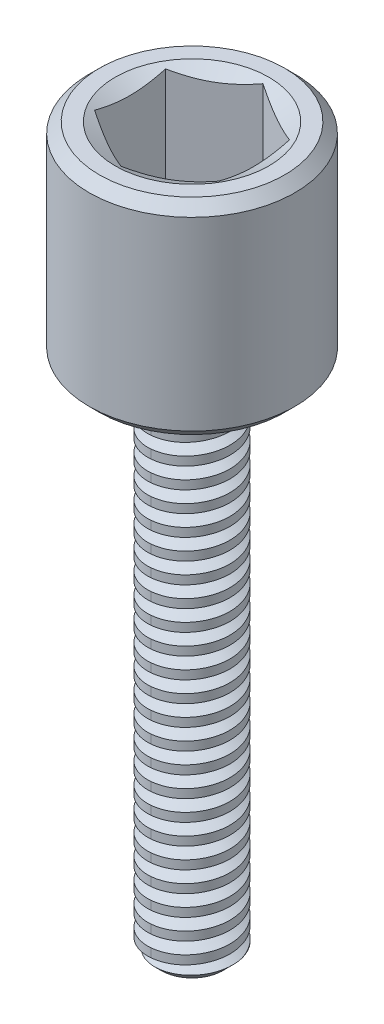
SolidWorks part; units mm, degrees
ref_plane "Front Plane" through (0, 0, 0) normal (0, 0, 1) x (1, 0, 0)
ref_plane "Top Plane" through (0, 0, 0) normal (0, 1, 0) x (1, 0, 0)
ref_plane "Right Plane" through (0, 0, 0) normal (1, 0, 0) x (0, 0, -1)
sketch "Sketch1" plane through (0, 0, 0) normal (0, 1, 0) x (1, 0, 0)
  circle A0 centre (0, 0) radius 2.54
extrude "Boss-Extrude1" add sketch "Sketch1" along normal blind 5.08
sketch "Sketch2" plane through (0, 0, 0) normal (0, -1, 0) x (1, 0, 0)
  circle A0 centre (0, 0) radius 1.016
extrude "Boss-Extrude2" add sketch "Sketch2" along normal blind 12.7
chamfer "Chamfer1" distance 0.254 angle 45 1 edges at (0, -12.7, -1.016)
sketch "Sketch4" plane through (0, -12.7, 0) normal (0, -1, 0) x (1, 0, 0)
  circle A0 centre (0, 0) radius 1.016 construction
  circle A1 centre (0, 0) radius 1.016
curve "Helix/Spiral1" pitch 0.508 height 12.7 turns 25
sketch "Sketch5" plane through (0, 0, 0) normal (1, 0, 0) x (0, 0, -1)
  line L0 (1.0802, -12.5163) -> (1.0802, -12.8837)
  line L1 (1.0802, -12.8837) -> (0.762, -12.7)
  line L2 (0.762, -12.7) -> (1.0802, -12.5163)
  line L3 (0, -12.2555) -> (0, -14.0004) construction
  spline S0 degree 3 poles (-0.7184, -12.7) (-0.8119, -12.6895) (-0.9634, -12.6682) (-1.0424, -12.6365) (-0.9631, -12.6047) (-0.7371, -12.573) (-0.3989, -12.5412) (0, -12.5095) (0.3989, -12.4777) (0.7371, -12.446) (0.9631, -12.4142) (1.0425, -12.3825) (0.9631, -12.3507) (0.7371, -12.319) (0.3989, -12.2872) (0, -12.2555) (-0.3989, -12.2237) (-0.7371, -12.192) (-0.9631, -12.1602) (-1.0425, -12.1285) (-0.9631, -12.0967) (-0.7371, -12.065) (-0.3989, -12.0332) (0, -12.0015) (0.3989, -11.9698) (0.7371, -11.938) (0.9631, -11.9062) (1.0425, -11.8745) (0.9631, -11.8428) (0.7371, -11.811) (0.3989, -11.7793) (0, -11.7475) (-0.3989, -11.7157) (-0.7371, -11.684) (-0.9631, -11.6523) (-1.0425, -11.6205) (-0.9631, -11.5888) (-0.7371, -11.557) (-0.3989, -11.5253) (0, -11.4935) (0.3989, -11.4618) (0.7371, -11.43) (0.9631, -11.3982) (1.0425, -11.3665) (0.9631, -11.3348) (0.7371, -11.303) (0.3989, -11.2713) (0, -11.2395) (-0.3989, -11.2078) (-0.7371, -11.176) (-0.9631, -11.1442) (-1.0425, -11.1125) (-0.9631, -11.0807) (-0.7371, -11.049) (-0.3989, -11.0172) (0, -10.9855) (0.3989, -10.9537) (0.7371, -10.922) (0.9631, -10.8902) (1.0425, -10.8585) (0.9631, -10.8267) (0.7371, -10.795) (0.3989, -10.7632) (0, -10.7315) (-0.3989, -10.6997) (-0.7371, -10.668) (-0.9631, -10.6362) (-1.0425, -10.6045) (-0.9631, -10.5727) (-0.7371, -10.541) (-0.3989, -10.5092) (0, -10.4775) (0.3989, -10.4457) (0.7371, -10.414) (0.9631, -10.3822) (1.0425, -10.3505) (0.9631, -10.3187) (0.7371, -10.287) (0.3989, -10.2552) (0, -10.2235) (-0.3989, -10.1917) (-0.7371, -10.16) (-0.9631, -10.1282) (-1.0425, -10.0965) (-0.9631, -10.0647) (-0.7371, -10.033) (-0.3989, -10.0012) (0, -9.9695) (0.3989, -9.9377) (0.7371, -9.906) (0.9631, -9.8742) (1.0425, -9.8425) (0.9631, -9.8107) (0.7371, -9.779) (0.3989, -9.7472) (0, -9.7155) (-0.3989, -9.6837) (-0.7371, -9.652) (-0.9631, -9.6202) (-1.0425, -9.5885) (-0.9631, -9.5567) (-0.7371, -9.525) (-0.3989, -9.4932) (0, -9.4615) (0.3989, -9.4297) (0.7371, -9.398) (0.9631, -9.3662) (1.0425, -9.3345) (0.9631, -9.3027) (0.7371, -9.271) (0.3989, -9.2392) (0, -9.2075) (-0.3989, -9.1757) (-0.7371, -9.144) (-0.9631, -9.1122) (-1.0425, -9.0805) (-0.9631, -9.0487) (-0.7371, -9.017) (-0.3989, -8.9852) (0, -8.9535) (0.3989, -8.9217) (0.7371, -8.89) (0.9631, -8.8582) (1.0425, -8.8265) (0.9631, -8.7947) (0.7371, -8.763) (0.3989, -8.7312) (0, -8.6995) (-0.3989, -8.6677) (-0.7371, -8.636) (-0.9631, -8.6042) (-1.0425, -8.5725) (-0.9631, -8.5407) (-0.7371, -8.509) (-0.3989, -8.4772) (0, -8.4455) (0.3989, -8.4137) (0.7371, -8.382) (0.9631, -8.3502) (1.0425, -8.3185) (0.9631, -8.2867) (0.7371, -8.255) (0.3989, -8.2232) (0, -8.1915) (-0.3989, -8.1597) (-0.7371, -8.128) (-0.9631, -8.0962) (-1.0425, -8.0645) (-0.9631, -8.0327) (-0.7371, -8.001) (-0.3989, -7.9693) (0, -7.9375) (0.3989, -7.9057) (0.7371, -7.874) (0.9631, -7.8423) (1.0425, -7.8105) (0.9631, -7.7788) (0.7371, -7.747) (0.3989, -7.7153) (0, -7.6835) (-0.3989, -7.6518) (-0.7371, -7.62) (-0.9631, -7.5883) (-1.0425, -7.5565) (-0.9631, -7.5248) (-0.7371, -7.493) (-0.3989, -7.4613) (0, -7.4295) (0.3989, -7.3978) (0.7371, -7.366) (0.9631, -7.3343) (1.0425, -7.3025) (0.9631, -7.2708) (0.7371, -7.239) (0.3989, -7.2073) (0, -7.1755) (-0.3989, -7.1438) (-0.7371, -7.112) (-0.9631, -7.0803) (-1.0425, -7.0485) (-0.9631, -7.0168) (-0.7371, -6.985) (-0.3989, -6.9533) (0, -6.9215) (0.3989, -6.8898) (0.7371, -6.858) (0.9631, -6.8263) (1.0425, -6.7945) (0.9631, -6.7628) (0.7371, -6.731) (0.3989, -6.6993) (0, -6.6675) (-0.3989, -6.6358) (-0.7371, -6.604) (-0.9631, -6.5723) (-1.0425, -6.5405) (-0.9631, -6.5088) (-0.7371, -6.477) (-0.3989, -6.4453) (0, -6.4135) (0.3989, -6.3818) (0.7371, -6.35) (0.9631, -6.3183) (1.0425, -6.2865) (0.9631, -6.2548) (0.7371, -6.223) (0.3989, -6.1913) (0, -6.1595) (-0.3989, -6.1278) (-0.7371, -6.096) (-0.9631, -6.0643) (-1.0425, -6.0325) (-0.9631, -6.0008) (-0.7371, -5.969) (-0.3989, -5.9373) (0, -5.9055) (0.3989, -5.8738) (0.7371, -5.842) (0.9631, -5.8103) (1.0425, -5.7785) (0.9631, -5.7468) (0.7371, -5.715) (0.3989, -5.6833) (0, -5.6515) (-0.3989, -5.6198) (-0.7371, -5.588) (-0.9631, -5.5563) (-1.0425, -5.5245) (-0.9631, -5.4928) (-0.7371, -5.461) (-0.3989, -5.4293) (0, -5.3975) (0.3989, -5.3658) (0.7371, -5.334) (0.9631, -5.3023) (1.0425, -5.2705) (0.9631, -5.2388) (0.7371, -5.207) (0.3989, -5.1753) (0, -5.1435) (-0.3989, -5.1118) (-0.7371, -5.08) (-0.9631, -5.0483) (-1.0425, -5.0165) (-0.9631, -4.9848) (-0.7371, -4.953) (-0.3989, -4.9213) (0, -4.8895) (0.3989, -4.8578) (0.7371, -4.826) (0.9631, -4.7943) (1.0425, -4.7625) (0.9631, -4.7308) (0.7371, -4.699) (0.3989, -4.6673) (0, -4.6355) (-0.3989, -4.6038) (-0.7371, -4.572) (-0.9631, -4.5403) (-1.0425, -4.5085) (-0.9631, -4.4768) (-0.7371, -4.445) (-0.3989, -4.4133) (0, -4.3815) (0.3989, -4.3498) (0.7371, -4.318) (0.9631, -4.2863) (1.0425, -4.2545) (0.9631, -4.2228) (0.7371, -4.191) (0.3989, -4.1593) (0, -4.1275) (-0.3989, -4.0958) (-0.7371, -4.064) (-0.9631, -4.0323) (-1.0425, -4.0005) (-0.9631, -3.9688) (-0.7371, -3.937) (-0.3989, -3.9053) (0, -3.8735) (0.3989, -3.8418) (0.7371, -3.81) (0.9631, -3.7783) (1.0425, -3.7465) (0.9631, -3.7148) (0.7371, -3.683) (0.3989, -3.6513) (0, -3.6195) (-0.3989, -3.5878) (-0.7371, -3.556) (-0.9631, -3.5243) (-1.0425, -3.4925) (-0.9631, -3.4608) (-0.7371, -3.429) (-0.3989, -3.3973) (0, -3.3655) (0.3989, -3.3338) (0.7371, -3.302) (0.9631, -3.2703) (1.0425, -3.2385) (0.9631, -3.2068) (0.7371, -3.175) (0.3989, -3.1433) (0, -3.1115) (-0.3989, -3.0798) (-0.7371, -3.048) (-0.9631, -3.0163) (-1.0425, -2.9845) (-0.9631, -2.9527) (-0.7371, -2.921) (-0.3989, -2.8893) (0, -2.8575) (0.3989, -2.8257) (0.7371, -2.794) (0.9631, -2.7622) (1.0425, -2.7305) (0.9631, -2.6987) (0.7371, -2.667) (0.3989, -2.6352) (0, -2.6035) (-0.3989, -2.5717) (-0.7371, -2.54) (-0.9631, -2.5082) (-1.0425, -2.4765) (-0.9631, -2.4447) (-0.7371, -2.413) (-0.3989, -2.3812) (0, -2.3495) (0.3989, -2.3177) (0.7371, -2.286) (0.9631, -2.2542) (1.0425, -2.2225) (0.9631, -2.1907) (0.7371, -2.159) (0.3989, -2.1272) (0, -2.0955) (-0.3989, -2.0637) (-0.7371, -2.032) (-0.9631, -2.0002) (-1.0425, -1.9685) (-0.9631, -1.9367) (-0.7371, -1.905) (-0.3989, -1.8732) (0, -1.8415) (0.3989, -1.8097) (0.7371, -1.778) (0.9631, -1.7462) (1.0425, -1.7145) (0.9631, -1.6827) (0.7371, -1.651) (0.3989, -1.6192) (0, -1.5875) (-0.3989, -1.5557) (-0.7371, -1.524) (-0.9631, -1.4922) (-1.0425, -1.4605) (-0.9631, -1.4287) (-0.7371, -1.397) (-0.3989, -1.3652) (0, -1.3335) (0.3989, -1.3017) (0.7371, -1.27) (0.9631, -1.2382) (1.0425, -1.2065) (0.9631, -1.1747) (0.7371, -1.143) (0.3989, -1.1112) (0, -1.0795) (-0.3989, -1.0477) (-0.7371, -1.016) (-0.9631, -0.9842) (-1.0425, -0.9525) (-0.9631, -0.9207) (-0.7371, -0.889) (-0.3989, -0.8572) (0, -0.8255) (0.3989, -0.7937) (0.7371, -0.762) (0.9631, -0.7302) (1.0425, -0.6985) (0.9631, -0.6667) (0.7371, -0.635) (0.3989, -0.6032) (0, -0.5715) (-0.3989, -0.5397) (-0.7371, -0.508) (-0.9631, -0.4763) (-1.0425, -0.4445) (-0.9631, -0.4128) (-0.7371, -0.381) (-0.3989, -0.3493) (0, -0.3175) (0.3989, -0.2858) (0.7371, -0.254) (0.9631, -0.2223) (1.0425, -0.1905) (0.9631, -0.1588) (0.7371, -0.127) (0.3989, -0.0953) (-0.0001, -0.0635) (-0.3987, -0.0318) (-0.625, -0.0105) (-0.7184, 0) knots 0 0 0 0 0.0025 0.005 0.0075 0.01 0.0125 0.015 0.0175 0.02 0.0225 0.025 0.0275 0.03 0.0325 0.035 0.0375 0.04 0.0425 0.045 0.0475 0.05 0.0525 0.055 0.0575 0.06 0.0625 0.065 0.0675 0.07 0.0725 0.075 0.0775 0.08 0.0825 0.085 0.0875 0.09 0.0925 0.095 0.0975 0.1 0.1025 0.105 0.1075 0.11 0.1125 0.115 0.1175 0.12 0.1225 0.125 0.1275 0.13 0.1325 0.135 0.1375 0.14 0.1425 0.145 0.1475 0.15 0.1525 0.155 0.1575 0.16 0.1625 0.165 0.1675 0.17 0.1725 0.175 0.1775 0.18 0.1825 0.185 0.1875 0.19 0.1925 0.195 0.1975 0.2 0.2025 0.205 0.2075 0.21 0.2125 0.215 0.2175 0.22 0.2225 0.225 0.2275 0.23 0.2325 0.235 0.2375 0.24 0.2425 0.245 0.2475 0.25 0.2525 0.255 0.2575 0.26 0.2625 0.265 0.2675 0.27 0.2725 0.275 0.2775 0.28 0.2825 0.285 0.2875 0.29 0.2925 0.295 0.2975 0.3 0.3025 0.305 0.3075 0.31 0.3125 0.315 0.3175 0.32 0.3225 0.325 0.3275 0.33 0.3325 0.335 0.3375 0.34 0.3425 0.345 0.3475 0.35 0.3525 0.355 0.3575 0.36 0.3625 0.365 0.3675 0.37 0.3725 0.375 0.3775 0.38 0.3825 0.385 0.3875 0.39 0.3925 0.395 0.3975 0.4 0.4025 0.405 0.4075 0.41 0.4125 0.415 0.4175 0.42 0.4225 0.425 0.4275 0.43 0.4325 0.435 0.4375 0.44 0.4425 0.445 0.4475 0.45 0.4525 0.455 0.4575 0.46 0.4625 0.465 0.4675 0.47 0.4725 0.475 0.4775 0.48 0.4825 0.485 0.4875 0.49 0.4925 0.495 0.4975 0.5 0.5025 0.505 0.5075 0.51 0.5125 0.515 0.5175 0.52 0.5225 0.525 0.5275 0.53 0.5325 0.535 0.5375 0.54 0.5425 0.545 0.5475 0.55 0.5525 0.555 0.5575 0.56 0.5625 0.565 0.5675 0.57 0.5725 0.575 0.5775 0.58 0.5825 0.585 0.5875 0.59 0.5925 0.595 0.5975 0.6 0.6025 0.605 0.6075 0.61 0.6125 0.615 0.6175 0.62 0.6225 0.625 0.6275 0.63 0.6325 0.635 0.6375 0.64 0.6425 0.645 0.6475 0.65 0.6525 0.655 0.6575 0.66 0.6625 0.665 0.6675 0.67 0.6725 0.675 0.6775 0.68 0.6825 0.685 0.6875 0.69 0.6925 0.695 0.6975 0.7 0.7025 0.705 0.7075 0.71 0.7125 0.715 0.7175 0.72 0.7225 0.725 0.7275 0.73 0.7325 0.735 0.7375 0.74 0.7425 0.745 0.7475 0.75 0.7525 0.755 0.7575 0.76 0.7625 0.765 0.7675 0.77 0.7725 0.775 0.7775 0.78 0.7825 0.785 0.7875 0.79 0.7925 0.795 0.7975 0.8 0.8025 0.805 0.8075 0.81 0.8125 0.815 0.8175 0.82 0.8225 0.825 0.8275 0.83 0.8325 0.835 0.8375 0.84 0.8425 0.845 0.8475 0.85 0.8525 0.855 0.8575 0.86 0.8625 0.865 0.8675 0.87 0.8725 0.875 0.8775 0.88 0.8825 0.885 0.8875 0.89 0.8925 0.895 0.8975 0.9 0.9025 0.905 0.9075 0.91 0.9125 0.915 0.9175 0.92 0.9225 0.925 0.9275 0.93 0.9325 0.935 0.9375 0.94 0.9425 0.945 0.9475 0.95 0.9525 0.955 0.9575 0.96 0.9625 0.965 0.9675 0.97 0.9725 0.975 0.9775 0.98 0.9825 0.985 0.9875 0.99 0.9925 0.995 0.9975 1 1 1 1 construction
  dimension "D1" = 60
  dimension "D2" = 0.762
sweep "Cut-Sweep1" cut profiles "Sketch5" path "Helix/Spiral1"
chamfer "Chamfer2" distance 0.254 angle 45 1 edges at (0, 0, 2.54)
sketch "Sketch6" plane through (0, 5.08, 0) normal (0, 1, 0) x (1, 0, 0)
  line L1 (1.5277, -0.8735) -> (1.5203, 0.8863)
  line L2 (1.5203, 0.8863) -> (-0.0074, 1.7597)
  line L3 (-0.0074, 1.7597) -> (-1.5277, 0.8735)
  line L4 (-1.5277, 0.8735) -> (-1.5203, -0.8863)
  line L5 (-1.5203, -0.8863) -> (0.0074, -1.7597)
  line L6 (0.0074, -1.7597) -> (1.5277, -0.8735)
  circle A0 centre (0, 0) radius 1.524 construction
extrude "Cut-Extrude1" cut sketch "Sketch6" against normal blind 3.81
chamfer "Chamfer3" distance 0.254 angle 45 1 edges at (0, 5.08, 2.54)
sketch "Sketch7" plane through (0, 0, 0) normal (1, 0, 0) x (0, 0, -1)
  line L0 (0, 5.08) -> (0, 0.254) construction
  line L1 (2.286, 5.08) -> (-2.286, 5.08) construction
  line L2 (-2.54, 0.254) -> (2.54, 0.254) construction
  line L3 (0, 5.08) -> (1.8985, 5.08)
  line L4 (1.8985, 5.08) -> (0, 4.064)
  line L5 (0, 4.064) -> (0, 5.08)
revolve "Cut-Revolve1" cut sketch "Sketch7" angle 360 about L5
